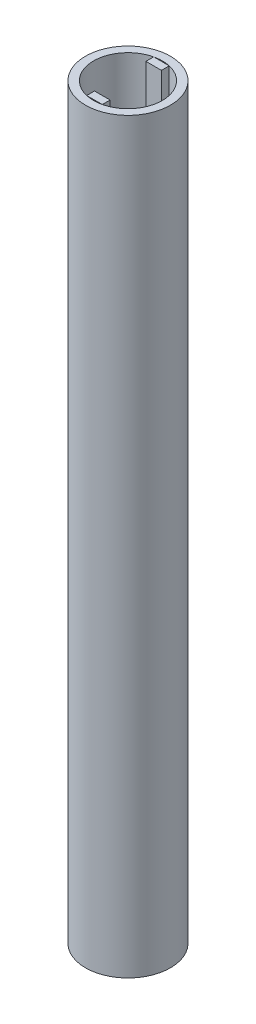
SolidWorks part; units mm, degrees
material "Acrylic (Medium-high impact)"
ref_plane "Front Plane" through (0, 0, 0) normal (0, 0, 1) x (1, 0, 0)
ref_plane "Top Plane" through (0, 0, 0) normal (0, 1, 0) x (1, 0, 0)
ref_plane "Right Plane" through (0, 0, 0) normal (1, 0, 0) x (0, 0, -1)
sketch "Sketch1" plane through (0, 0, 0) normal (0, 1, 0) x (1, 0, 0)
  circle A0 centre (0, 0) radius 28.0416
  circle A1 centre (0, 0) radius 34.6583
  dimension "D1" = 69.3166
  dimension "D2" = 56.0832
extrude "Boss-Extrude1" add sketch "Sketch1" along normal blind 609.6
sketch "Sketch2" plane through (0, 0, 0) normal (0, -1, 0) x (1, 0, 0)
  circle A0 centre (0, 0) radius 28.0416
  circle A1 centre (0, 0) radius 30.7189
  dimension "D1" = 61.4378
extrude "Cut-Extrude1" [suppressed] cut sketch "Sketch2" against normal blind 50.8
sketch "Sketch3" plane through (0, 609.6, 0) normal (0, 1, 0) x (1, 0, 0)
  line L1 (-6.35, 27.3132) -> (6.35, 27.3132)
  line L2 (-6.35, 27.3132) -> (-6.35, 20.9632)
  line L3 (-6.35, 20.9632) -> (6.35, 20.9632)
  line L4 (6.35, 27.3132) -> (6.35, 20.9632)
  circle A0 centre (0, 0) radius 28.0416 construction
  dimension "D1" = 12.7
  dimension "D2" = 6.35
  dimension "D3" = 28.0416
  dimension "D4" = 6.35
extrude "Boss-Extrude3" add sketch "Sketch3" against normal blind 127 separate body
sketch "Sketch4" plane through (0, 0, -20.9632) normal (0, 0, 1) x (1, 0, 0)
  line L0 (6.35, 482.6) -> (-6.35, 482.6)
  line L1 (6.35, 482.6) -> (6.35, 609.6) construction
  line L2 (-6.35, 482.6) -> (-6.35, 495.3)
  line L3 (-6.35, 482.6) -> (-6.35, 609.6) construction
  line L4 (-6.35, 495.3) -> (6.35, 482.6)
  dimension "D1" = 12.7
extrude "Cut-Extrude2" cut sketch "Sketch4" against normal up to next (6.35 mm away)
pattern_circular "CirPattern8" count 2 over 360 about axis through (0, 0, 0) along (0, 1, 0) of bodies 105
equation "\"D2@Sketch3\" = \"D1@Sketch3\"/2"
equation "\"D3@Sketch3\" = \"D2@Sketch1\"/2"
equation "\"D1@Sketch4\" = \"D1@Sketch3\""
